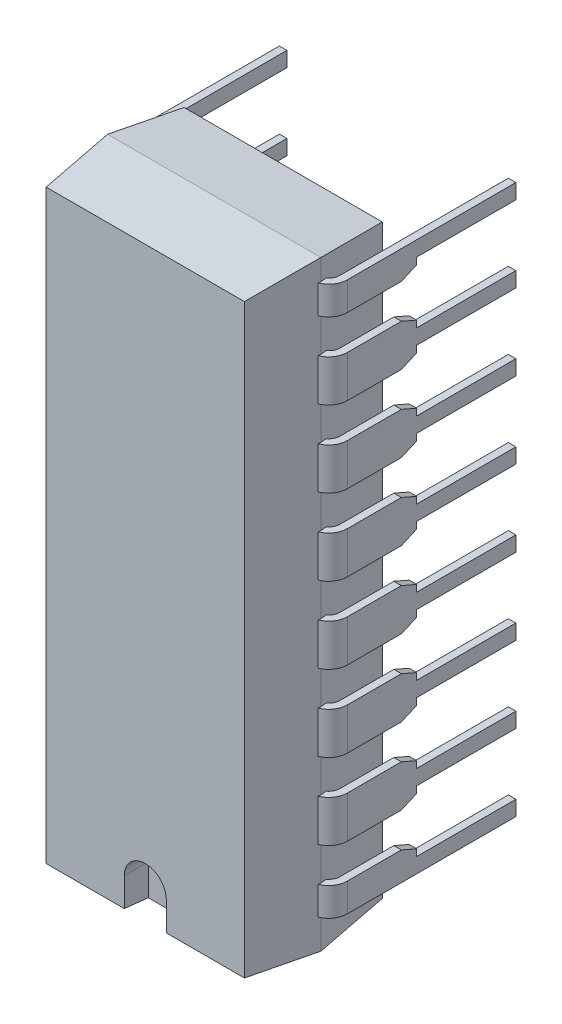
SolidWorks part; units mm, degrees
ref_plane "Front Plane" through (0, 0, 0) normal (0, 0, 1) x (1, 0, 0)
ref_plane "Top Plane" through (0, 0, 0) normal (0, 1, 0) x (1, 0, 0)
ref_plane "Right Plane" through (0, 0, 0) normal (1, 0, 0) x (0, 0, -1)
sketch "Sketch1" plane through (0, 0, 0) normal (0, 1, 0) x (1, 0, 0)
  line L0 (-3.3, -5.1) -> (-3.55, -2.805)
  line L1 (-3.55, -2.805) -> (3.55, -2.805) construction
  line L2 (3.55, -2.805) -> (3.3, -5.1)
  line L3 (3.3, -5.1) -> (-3.3, -5.1)
  line L4 (-3.55, -2.805) -> (-3.3, -0.51)
  line L5 (-3.3, -0.51) -> (3.3, -0.51)
  line L6 (3.3, -0.51) -> (3.55, -2.805)
  line L7 (0, 0) -> (3.3, 0) construction
  line L8 (0, -0.51) -> (0, -5.1) construction
  point P11 (0, -2.805)
  point P12 (0, -5.1)
  point P13 (0, -0.51)
  dimension "D1" = 0.51
  dimension "F" = 7.1
  dimension "D2" = 5.1
  dimension "D4" = 6.6
extrude "Basic Shape" add sketch "Sketch1" along normal mid plane 20
sketch "Sketch2" plane through (0, 0, 0) normal (1, 0, 0) x (0, 0, -1)
  line L1 (-0.51, -10) -> (-2.805, -10) construction
  line L2 (-0.51, 10) -> (-0.51, -10) construction
  line L3 (-0.51, 10) -> (-0.51, 9.75)
  line L4 (-0.51, 10) -> (-2.805, 10) construction
  line L5 (-0.51, 10) -> (-2.805, 10)
  line L6 (-2.805, 10) -> (-0.51, 9.75)
  line L7 (-0.51, -10) -> (-2.805, -10)
  line L9 (-2.805, -10) -> (-0.51, -9.75)
  line L11 (-0.51, -9.75) -> (-0.51, -10)
  dimension "D1" = 0.25
extrude "Side Profile1" cut sketch "Sketch2" against normal through all and the other way through all
sketch "Sketch3" plane through (0, 0, 0) normal (1, 0, 0) x (0, 0, -1)
  line L0 (-2.805, 10) -> (-5.1, 10) construction
  line L1 (-2.805, 10) -> (-5.1, 10)
  line L2 (-5.1, 10) -> (-5.1, -10) construction
  line L3 (-5.1, 10) -> (-5.1, 9.75)
  line L4 (-2.805, 10) -> (-5.1, 9.75)
  line L5 (-2.805, -10) -> (-5.1, -10) construction
  line L6 (-2.805, -10) -> (-5.1, -10)
  line L7 (-2.805, -10) -> (-5.1, -9.75)
  line L8 (-5.1, -9.75) -> (-5.1, -10)
extrude "Side Profile2" cut sketch "Sketch3" against normal through all and the other way through all
sketch "First Pin Location" plane through (0, 0, 0) normal (1, 0, 0) x (0, 0, -1)
  line L0 (-2.805, 10) -> (-2.805, -10) construction
  point P0 (-2.805, -10)
  point P1 (-2.805, -8.73)
  dimension "Z" = 1.27
ref_plane "First Pin Plane" through (0, -8.73, 0) normal (0, 1, 0) x (-1, 0, 0)
sketch "Sketch4" plane through (0, 0, 5.1) normal (0, 0, 1) x (1, 0, 0)
  line L2 (-0.7, -10) -> (-0.7, -8.8)
  line L3 (0.7, -8.8) -> (0.7, -10)
  line L4 (-3.55, -10) -> (3.55, -10) construction
  line L5 (-0.7, -10) -> (0.7, -10)
  arc A0 (-0.7, -8.8) -> (0.7, -8.8) centre (0, -8.8) cw
  dimension "D1" = 1.2
  dimension "D2" = 1.4
extrude "Location Mark" cut sketch "Sketch4" against normal blind 0.8
sketch "Sketch5" plane through (0, -8.73, 0) normal (0, 1, 0) x (1, 0, 0)
  line L0 (-3.55, -2.805) -> (3.55, -2.805) construction
  line L1 (0, -2.805) -> (3.31, -2.805)
  line L2 (3.81, -2.305) -> (3.81, 3.3)
  line L3 (3.81, -2.805) -> (-3.81, -2.805) construction
  arc A0 (3.81, -2.305) -> (3.31, -2.805) centre (3.31, -2.305) cw
  point P0 (-3.81, -2.805)
  point P8 (0, -2.805)
  dimension "D3" = 3.3
  dimension "D2" = 0.5
  dimension "D1" = 7.62
sketch "Sketch6" plane through (0, 0, 0) normal (1, 0, 0) x (0, 0, -1)
  line L0 (-2.93, -8.035) -> (-2.68, -8.035)
  line L1 (-2.93, -8.035) -> (-2.93, -9.425)
  line L2 (-2.68, -9.425) -> (-2.93, -9.425)
  line L3 (-2.68, -9.425) -> (-2.68, -8.035)
  line L4 (-2.68, -8.035) -> (-2.93, -9.425) construction
  point P4 (-2.805, -8.73)
  dimension "D1" = 1.39
  dimension "D2" = 0.25
sweep "First Pin" add profiles "Sketch6" path "Sketch5"
sketch "Sketch7" plane through (3.685, 0, 0) normal (-1, 0, 0) x (0, 0, 1)
  line L0 (-3.3, -9.425) -> (-3.3, -8.035) construction
  line L1 (-3.3, -8.035) -> (-3.3, -9.425) construction
  line L2 (-3.3, -8.98) -> (-3.3, -8.48) construction
  line L3 (-3.3, -8.98) -> (0, -8.98)
  line L4 (0.51, 9.75) -> (0.51, -9.75) construction
  line L5 (-3.3, -8.48) -> (0, -8.48)
  line L6 (0, -8.48) -> (0, -8.2575)
  line L7 (0, -8.98) -> (0, -9.2025)
  line L8 (2.305, -8.035) -> (-3.3, -8.035) construction
  line L9 (0.51, -8.035) -> (-3.3, -8.035)
  line L10 (2.305, -9.425) -> (-3.3, -9.425) construction
  line L11 (0.51, -9.425) -> (-3.3, -9.425)
  line L12 (-3.3, -8.98) -> (-3.3, -9.425)
  line L13 (-3.3, -8.035) -> (-3.3, -8.48)
  line L14 (0, -9.2025) -> (0.51, -9.425)
  line L16 (0, -8.2575) -> (0.51, -8.035)
  point P10 (-3.3, -8.2575)
  dimension "D1" = 0.5
extrude "Pin Relief" cut sketch "Sketch7" against normal through all
mirror "Opp Pin" about plane through (0, 0, 0) normal (1, 0, 0) of "Pin Relief", "First Pin"
pattern_linear "Remaining Pins" count 8 spacing 2.54 along (0, 1, 0) of "First Pin", "Opp Pin", "Pin Relief"
sketch "Sketch9" plane through (0, -9.425, 0) normal (0, -1, 0) x (1, 0, 0)
  line L0 (3.935, 0) -> (3.685, 0) construction
  line L1 (3.935, 0) -> (3.685, 0)
  line L2 (-3.935, 0) -> (-3.685, 0) construction
  line L3 (-3.935, 0) -> (-3.685, 0)
  line L7 (3.685, 2.305) -> (3.685, 0.51)
  line L8 (3.685, 0.51) -> (3.935, 0.51)
  line L9 (3.935, 0.51) -> (3.935, 2.305)
  line L11 (3.5412, 2.8857) -> (3.55, 2.805)
  line L12 (3.55, 2.805) -> (3.5287, 2.6096)
  line L14 (3.685, 2.305) -> (3.685, 0)
  line L16 (3.935, 0) -> (3.935, 2.305)
  line L18 (3.5412, 2.8857) -> (3.55, 2.805)
  line L19 (3.55, 2.805) -> (3.5287, 2.6096)
  line L22 (-3.685, 0.51) -> (-3.685, 2.305)
  line L24 (-3.5287, 2.6096) -> (-3.55, 2.805)
  line L25 (-3.55, 2.805) -> (-3.5412, 2.8857)
  line L27 (-3.935, 2.305) -> (-3.935, 0.51)
  line L28 (-3.935, 0.51) -> (-3.685, 0.51)
  line L29 (-3.685, 0) -> (-3.685, 2.305)
  line L31 (-3.5287, 2.6096) -> (-3.55, 2.805)
  line L32 (-3.55, 2.805) -> (-3.5412, 2.8857)
  line L34 (-3.935, 2.305) -> (-3.935, 0)
  arc A2 (3.935, 2.305) -> (3.5412, 2.8857) centre (3.31, 2.305) ccw
  arc A3 (3.935, 2.305) -> (3.5412, 2.8857) centre (3.31, 2.305) ccw
  arc A4 (3.685, 2.305) -> (3.5287, 2.6096) centre (3.31, 2.305) ccw
  arc A5 (3.685, 2.305) -> (3.5287, 2.6096) centre (3.31, 2.305) ccw
  arc A6 (-3.5287, 2.6096) -> (-3.685, 2.305) centre (-3.31, 2.305) ccw
  arc A7 (-3.5287, 2.6096) -> (-3.685, 2.305) centre (-3.31, 2.305) ccw
  arc A8 (-3.5412, 2.8857) -> (-3.935, 2.305) centre (-3.31, 2.305) ccw
  arc A9 (-3.5412, 2.8857) -> (-3.935, 2.305) centre (-3.31, 2.305) ccw
  dimension "D1" = 0
  dimension "D2" = 0
extrude "Pin Relief1" cut sketch "Sketch9" against normal up to surface (0.445 mm away) up to face at (-3.81, -8.98, -1.65)
sketch "Sketch10" plane through (0, 9.745, 0) normal (0, 1, 0) x (-1, 0, 0)
  line L0 (3.935, 0) -> (3.685, 0) construction
  line L1 (3.935, 0) -> (3.685, 0)
  line L2 (-3.935, 0) -> (-3.685, 0) construction
  line L3 (-3.935, 0) -> (-3.685, 0)
  line L7 (3.685, 0.51) -> (3.935, 0.51)
  line L8 (3.935, 0.51) -> (3.935, 2.305)
  line L10 (3.5412, 2.8857) -> (3.55, 2.805)
  line L11 (3.55, 2.805) -> (3.5287, 2.6096)
  line L13 (3.685, 2.305) -> (3.685, 0.51)
  line L14 (-3.935, 0.51) -> (-3.685, 0.51)
  line L15 (3.935, 0) -> (3.935, 2.305)
  line L16 (-3.685, 0.51) -> (-3.685, 2.305)
  line L17 (3.5412, 2.8857) -> (3.55, 2.805)
  line L18 (3.55, 2.805) -> (3.5287, 2.6096)
  line L19 (-3.5287, 2.6096) -> (-3.55, 2.805)
  line L20 (3.685, 2.305) -> (3.685, 0)
  line L21 (-3.55, 2.805) -> (-3.5412, 2.8857)
  line L22 (-3.935, 2.305) -> (-3.935, 0.51)
  line L24 (-3.685, 0) -> (-3.685, 2.305)
  line L25 (-3.5287, 2.6096) -> (-3.55, 2.805)
  line L26 (-3.55, 2.805) -> (-3.5412, 2.8857)
  line L27 (-3.935, 2.305) -> (-3.935, 0)
  arc A2 (3.935, 2.305) -> (3.5412, 2.8857) centre (3.31, 2.305) ccw
  arc A3 (3.935, 2.305) -> (3.5412, 2.8857) centre (3.31, 2.305) ccw
  arc A4 (3.685, 2.305) -> (3.5287, 2.6096) centre (3.31, 2.305) ccw
  arc A5 (3.685, 2.305) -> (3.5287, 2.6096) centre (3.31, 2.305) ccw
  arc A6 (-3.5287, 2.6096) -> (-3.685, 2.305) centre (-3.31, 2.305) ccw
  arc A7 (-3.5412, 2.8857) -> (-3.935, 2.305) centre (-3.31, 2.305) ccw
  arc A8 (-3.5287, 2.6096) -> (-3.685, 2.305) centre (-3.31, 2.305) ccw
  arc A9 (-3.5412, 2.8857) -> (-3.935, 2.305) centre (-3.31, 2.305) ccw
  dimension "D1" = 0
  dimension "D2" = 0
extrude "Pin Relief2" cut sketch "Sketch10" against normal up to surface (0.445 mm away) up to face at (-3.81, 9.3, -1.65)
sketch "Component_Outline" plane through (0, 0, 0) normal (0, 0, 1) x (1, 0, 0)
  line L0 (3.55, 10) -> (3.55, 9.3)
  line L1 (3.55, 9.3) -> (3.935, 9.3)
  line L2 (3.935, 9.3) -> (3.935, 8.355)
  line L3 (3.935, 8.355) -> (3.55, 8.355)
  line L4 (3.55, 8.355) -> (3.55, 7.205)
  line L5 (3.55, 7.205) -> (3.935, 7.205)
  line L6 (3.935, 7.205) -> (3.935, 5.815)
  line L7 (3.935, 5.815) -> (3.55, 5.815)
  line L8 (3.55, 5.815) -> (3.55, 4.665)
  line L9 (3.55, 4.665) -> (3.935, 4.665)
  line L10 (3.935, 4.665) -> (3.935, 3.275)
  line L11 (3.935, 3.275) -> (3.55, 3.275)
  line L12 (3.55, 3.275) -> (3.55, 2.125)
  line L13 (3.55, 2.125) -> (3.935, 2.125)
  line L14 (3.935, 2.125) -> (3.935, 0.735)
  line L15 (3.935, 0.735) -> (3.55, 0.735)
  line L16 (3.55, 0.735) -> (3.55, -0.415)
  line L17 (3.55, -0.415) -> (3.935, -0.415)
  line L18 (3.935, -0.415) -> (3.935, -1.805)
  line L19 (3.935, -1.805) -> (3.55, -1.805)
  line L20 (3.55, -1.805) -> (3.55, -2.955)
  line L21 (3.55, -2.955) -> (3.935, -2.955)
  line L22 (3.935, -2.955) -> (3.935, -4.345)
  line L23 (3.935, -4.345) -> (3.55, -4.345)
  line L24 (3.55, -4.345) -> (3.55, -5.495)
  line L25 (3.55, -5.495) -> (3.935, -5.495)
  line L26 (3.935, -5.495) -> (3.935, -6.885)
  line L27 (3.935, -6.885) -> (3.55, -6.885)
  line L28 (3.55, -6.885) -> (3.55, -8.035)
  line L29 (3.55, -8.035) -> (3.935, -8.035)
  line L30 (3.935, -8.035) -> (3.935, -8.98)
  line L31 (3.935, -8.98) -> (3.55, -8.98)
  line L32 (3.55, -8.98) -> (3.55, -10)
  line L33 (0, 10) -> (0, -10) construction
  line L34 (-3.55, 10) -> (3.55, 10) construction
  line L35 (-3.55, -10) -> (3.55, -10) construction
  line L36 (-3.55, -8.98) -> (-3.55, -10)
  line L37 (-3.935, -8.98) -> (-3.55, -8.98)
  line L38 (-3.935, -8.035) -> (-3.935, -8.98)
  line L39 (-3.55, -8.035) -> (-3.935, -8.035)
  line L40 (-3.55, -6.885) -> (-3.55, -8.035)
  line L41 (-3.935, -6.885) -> (-3.55, -6.885)
  line L42 (-3.935, -5.495) -> (-3.935, -6.885)
  line L43 (-3.55, -5.495) -> (-3.935, -5.495)
  line L44 (-3.55, -4.345) -> (-3.55, -5.495)
  line L45 (-3.935, -4.345) -> (-3.55, -4.345)
  line L46 (-3.935, -2.955) -> (-3.935, -4.345)
  line L47 (-3.55, -2.955) -> (-3.935, -2.955)
  line L48 (-3.55, -1.805) -> (-3.55, -2.955)
  line L49 (-3.935, -1.805) -> (-3.55, -1.805)
  line L50 (-3.935, -0.415) -> (-3.935, -1.805)
  line L51 (-3.55, -0.415) -> (-3.935, -0.415)
  line L52 (-3.55, 0.735) -> (-3.55, -0.415)
  line L53 (-3.935, 0.735) -> (-3.55, 0.735)
  line L54 (-3.935, 2.125) -> (-3.935, 0.735)
  line L55 (-3.55, 2.125) -> (-3.935, 2.125)
  line L56 (-3.55, 3.275) -> (-3.55, 2.125)
  line L57 (-3.935, 3.275) -> (-3.55, 3.275)
  line L58 (-3.935, 4.665) -> (-3.935, 3.275)
  line L59 (-3.55, 4.665) -> (-3.935, 4.665)
  line L60 (-3.55, 5.815) -> (-3.55, 4.665)
  line L61 (-3.935, 5.815) -> (-3.55, 5.815)
  line L62 (-3.935, 7.205) -> (-3.935, 5.815)
  line L63 (-3.55, 7.205) -> (-3.935, 7.205)
  line L64 (-3.55, 8.355) -> (-3.55, 7.205)
  line L65 (-3.935, 8.355) -> (-3.55, 8.355)
  line L66 (-3.935, 9.3) -> (-3.935, 8.355)
  line L67 (-3.55, 9.3) -> (-3.935, 9.3)
  line L68 (-3.55, 10) -> (-3.55, 9.3)
  line L69 (3.55, 10) -> (-3.55, 10)
  line L70 (-3.55, -10) -> (3.55, -10)
  line L71 (3.935, -8.98) -> (3.55, -8.035) construction
  point P108 (3.7425, -8.5075)
